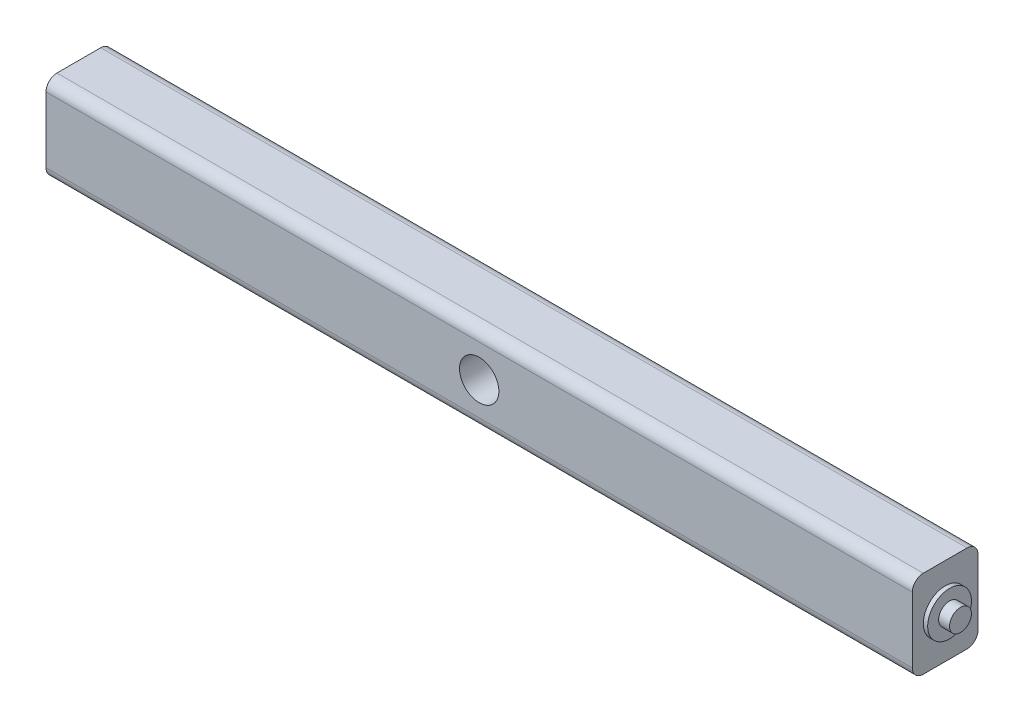
SolidWorks part; units mm, degrees
material "Plain Carbon Steel"
ref_plane "Front Plane" through (0, 0, 0) normal (0, 0, 1) x (1, 0, 0)
ref_plane "Top Plane" through (0, 0, 0) normal (0, 1, 0) x (1, 0, 0)
ref_plane "Right Plane" through (0, 0, 0) normal (1, 0, 0) x (0, 0, -1)
sketch "Sketch1" plane through (0, 0, 0) normal (1, 0, 0) x (0, 0, -1)
  circle A0 centre (0, 0) radius 10
  dimension "D1" = 20
extrude "Boss-Extrude1" add sketch "Sketch1" along normal mid plane 410
sketch "Sketch2" plane through (-205, 0, 0) normal (-1, 0, 0) x (0, 0, 1)
  circle A0 centre (0, 0) radius 5
  circle A1 centre (0, 0) radius 12.5
  dimension "D1" = 10
  dimension "D2" = 25
extrude "Cut-Extrude1" cut sketch "Sketch2" against normal blind 5
mirror "Mirror1" about plane through (0, 0, 0) normal (1, 0, 0) of "Cut-Extrude1"
sketch "Sketch3" plane through (0, 0, 0) normal (0, 0, 1) x (1, 0, 0)
  line L1 (-20, 20) -> (20, 20)
  line L2 (-20, 20) -> (-20, -20)
  line L3 (-20, -20) -> (20, -20)
  line L4 (20, 20) -> (20, -20)
  point P0 (0, 0)
  dimension "D1" = 40
  dimension "D2" = 40
extrude "Boss-Extrude5" add sketch "Sketch3" along normal mid plane 30 contours L1 L4 L3 L2
sketch "Sketch4" plane through (0, 0, 0) normal (0, 0, 1) x (1, 0, 0)
  circle A0 centre (0, 0) radius 9
  dimension "D1" = 18
extrude "Cut-Extrude2" cut sketch "Sketch4" against normal mid plane 30
cosmetic thread "Cosmetic Thread1" parameters "D2"=20
fillet "Fillet2" radius 2 2 edges at (20, 0, -10) (-20, 10, 0)
sketch "Sketch5" plane through (-20, 0, 0) normal (-1, 0, 0) x (0, 0, 1)
  line L1 (-15, 20) -> (15, 20)
  line L2 (-15, 20) -> (-15, -20)
  line L3 (-15, -20) -> (15, -20)
  line L4 (15, 20) -> (15, -20)
extrude "Boss-Extrude6" add sketch "Sketch5" along normal blind 178
sketch "Sketch6" plane through (20, 0, 0) normal (1, 0, 0) x (0, 0, -1)
  line L1 (-15, 20) -> (15, 20)
  line L2 (-15, 20) -> (-15, -20)
  line L3 (-15, -20) -> (15, -20)
  line L4 (15, 20) -> (15, -20)
extrude "Boss-Extrude7" add sketch "Sketch6" along normal blind 178
fillet "Fillet3" radius 5 4 edges at (0, 20, -15) (0, -20, -15) (0, -20, 15) (0, 20, 15)
